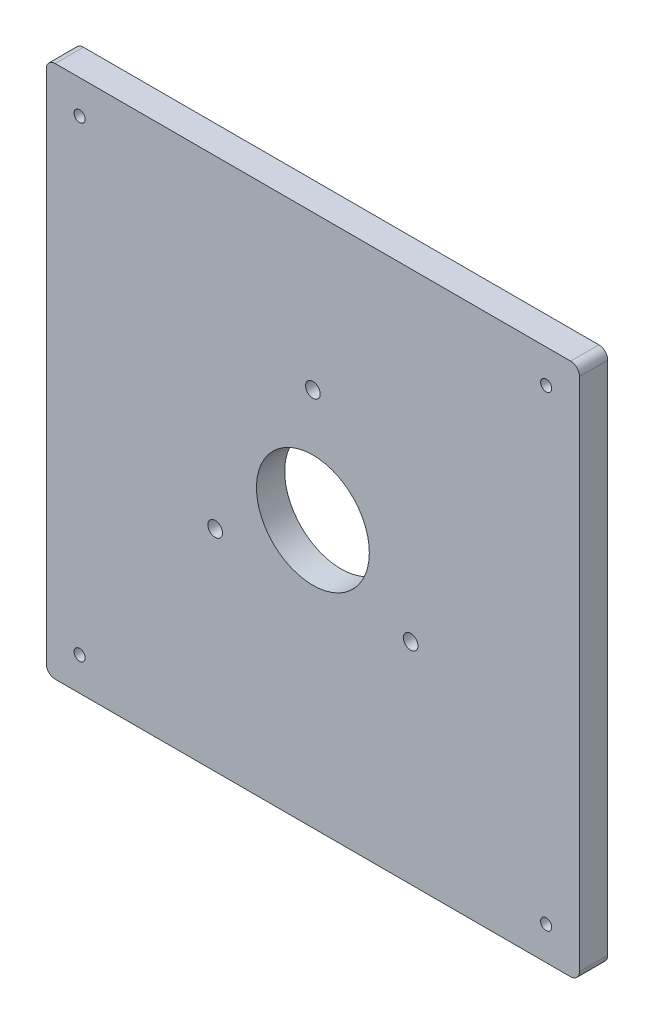
SolidWorks part; units mm, degrees
material "6061-T6 (SS)"
ref_plane "Plan de face" through (0, 0, 0) normal (0, 0, 1) x (1, 0, 0)
ref_plane "Plan de dessus" through (0, 0, 0) normal (0, 1, 0) x (1, 0, 0)
ref_plane "Plan de droite" through (0, 0, 0) normal (1, 0, 0) x (0, 0, -1)
sketch "Esquisse1" plane through (0, 0, 0) normal (0, 0, 1) x (1, 0, 0)
  line L0 (60, 120) -> (60, 0) construction
  line L1 (0, 0) -> (120, 0)
  line L2 (0, 0) -> (0, 120)
  line L3 (0, 120) -> (120, 120)
  line L4 (120, 0) -> (120, 120)
  line L5 (0, 60) -> (120, 60) construction
  line L6 (0, 120) -> (120, 0) construction
  circle A0 centre (7.5, 112.5) radius 1.25
  circle A1 centre (112.5, 112.5) radius 1.25
  circle A2 centre (112.5, 7.5) radius 1.25
  circle A3 centre (7.5, 7.5) radius 1.25
  circle A4 centre (60, 60) radius 12.7
  dimension "D2" = 2.5
  dimension "D4" = 25.4
  dimension "D1" = 120
  dimension "D3" = 7.5
extrude "Boss.-Extru.1" add sketch "Esquisse1" along normal blind 6.35
fillet "Congé1" radius 2 4 edges at (0, 0, 3.175) (120, 0, 3.175) (0, 120, 3.175) (120, 120, 3.175)
sketch "Esquisse2" plane through (0, 0, 6.35) normal (0, 0, 1) x (1, 0, 0)
  line L0 (60, 120) -> (60, 0) construction
  line L1 (118, 120) -> (2, 120) construction
  line L2 (2, 0) -> (118, 0) construction
  line L3 (0, 60) -> (120, 60) construction
  line L4 (0, 118) -> (0, 2) construction
  line L5 (120, 2) -> (120, 118) construction
  line L6 (38.003, 47.3) -> (60, 60) construction
  line L7 (81.997, 47.3) -> (60, 60) construction
  circle A0 centre (60, 60) radius 25.4
  circle A1 centre (60, 85.4) radius 1.65
  circle A2 centre (38.003, 47.3) radius 1.65
  circle A3 centre (81.997, 47.3) radius 1.65
  dimension "D1" = 50.8
  dimension "D2" = 3.3
  dimension "D3" = 120
  dimension "D4" = 120
extrude "Enlèv. mat.-Extru.1" cut sketch "Esquisse2" against normal through all contours A3 | A2 | A1
